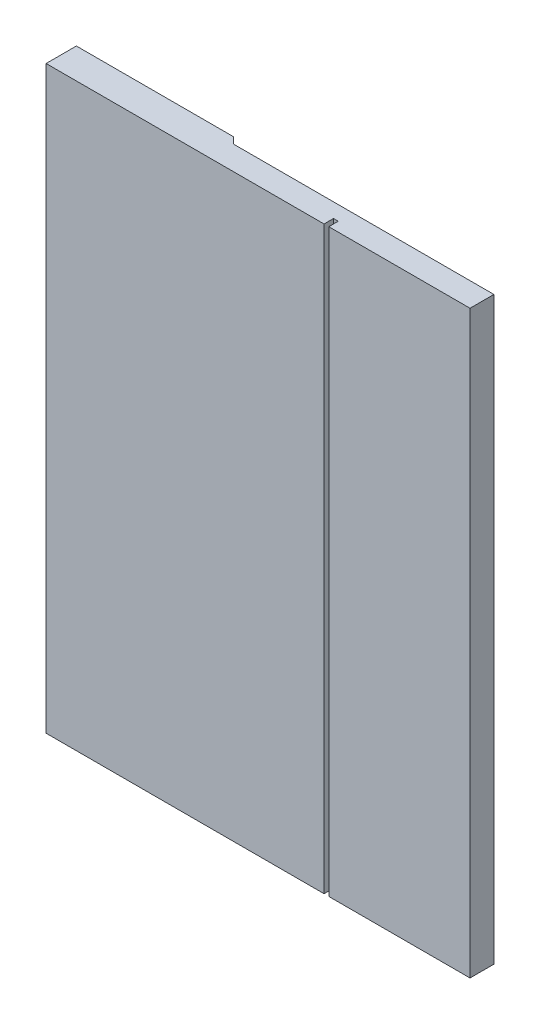
SolidWorks part; units mm, degrees
material "6061 Alloy"
ref_plane "Front Plane" through (0, 0, 0) normal (0, 0, 1) x (1, 0, 0)
ref_plane "Top Plane" through (0, 0, 0) normal (0, 1, 0) x (1, 0, 0)
ref_plane "Right Plane" through (0, 0, 0) normal (1, 0, 0) x (0, 0, -1)
sketch "Sketch1" plane through (0, 0, 0) normal (0, 1, 0) x (1, 0, 0)
  line L0 (-4.75, 15) -> (-4.75, 5.05)
  line L1 (0, 0) -> (-31.25, 0)
  line L2 (0, 0) -> (0, 15)
  line L3 (0, 15) -> (-4.75, 15)
  line L4 (-91, 0) -> (-91, 6.4)
  line L5 (-4.75, 5.05) -> (-14.75, 5.05)
  line L6 (-14.75, 5.05) -> (-14.75, 6.4)
  line L7 (-14.75, 6.4) -> (-91, 6.4)
  line L8 (-32.25, 0) -> (-32.25, 2)
  line L9 (-32.25, 2) -> (-31.25, 2)
  line L10 (-31.25, 2) -> (-31.25, 0)
  line L11 (-32.25, 0) -> (-91, 0)
  dimension "D1" = 91
  dimension "D2" = 6.4
  dimension "D3" = 1.35
  dimension "D4" = 15
  dimension "D5" = 4.75
  dimension "D6" = 10
  dimension "D7" = 1
  dimension "D8" = 31.25
  dimension "D9" = 2
extrude "Boss-Extrude1" add sketch "Sketch1" along normal blind 122.6
sketch "Sketch2" plane through (0, 0, 0) normal (1, 0, 0) x (0, 0, -1)
  line L1 (30.5401, -12.6484) -> (-22.3165, -12.6484)
  line L2 (30.5401, -12.6484) -> (30.5401, 124.2366)
  line L3 (30.5401, 124.2366) -> (-22.3165, 124.2366)
  line L4 (-22.3165, -12.6484) -> (-22.3165, 124.2366)
  line L5 (30.5401, -12.6484) -> (-22.3165, 124.2366) construction
  line L6 (30.5401, 124.2366) -> (-22.3165, -12.6484) construction
  point P0 (4.1118, 55.7941)
extrude "Cut-Extrude1" cut sketch "Sketch2" against normal offset from surface (1.4 mm away) 89.6 up to face at (-91, 61.3, -3.2)
sketch "Sketch3" plane through (0, 122.6, 0) normal (0, 1, 0) x (1, 0, 0)
  line L0 (-1.4, 5.05) -> (-56.4, 5.05)
  line L1 (-1.4, 0) -> (-1.4, 15) construction
  line L2 (-56.4, 5.05) -> (-60.8211, 9.4711)
  line L3 (-60.8211, 9.4711) -> (-60.8211, 21.0137)
  line L4 (-60.8211, 21.0137) -> (-1.4, 21.0137)
  line L5 (-1.4, 21.0137) -> (-1.4, 5.05)
  dimension "D1" = 55
  dimension "D2" = 135
extrude "Cut-Extrude2" cut sketch "Sketch3" against normal through all both and the other way through all
